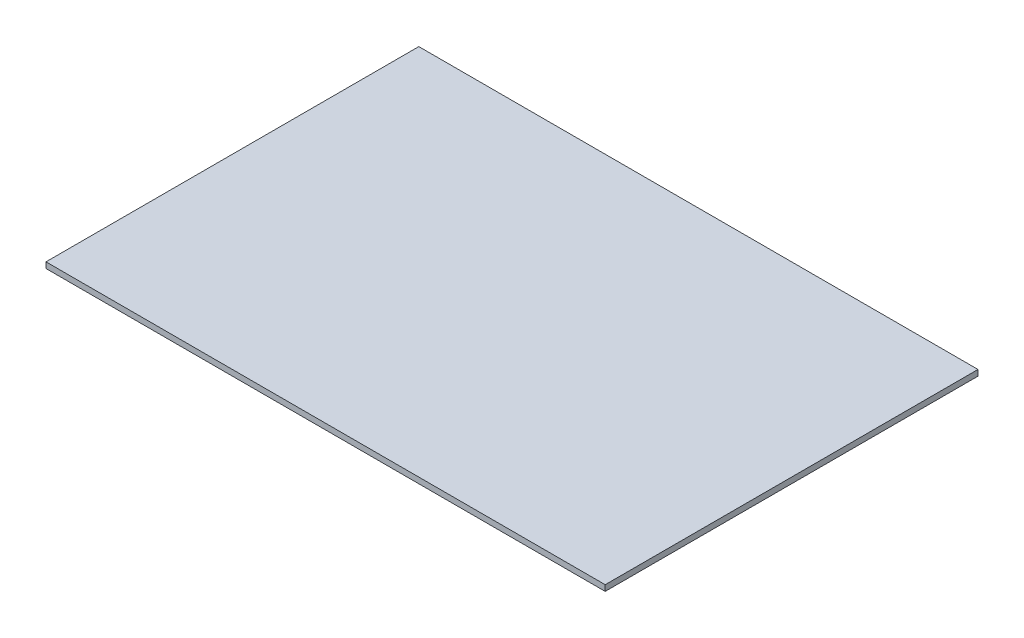
SolidWorks part; units mm, degrees
ref_plane "Front Plane" through (0, 0, 0) normal (0, 0, 1) x (1, 0, 0)
ref_plane "Top Plane" through (0, 0, 0) normal (0, 1, 0) x (1, 0, 0)
ref_plane "Right Plane" through (0, 0, 0) normal (1, 0, 0) x (0, 0, -1)
sketch "Sketch1" plane through (0, 0, 0) normal (0, 1, 0) x (1, 0, 0)
  line L1 (152.4, -101.6) -> (-152.4, -101.6)
  line L2 (152.4, -101.6) -> (152.4, 101.6)
  line L3 (152.4, 101.6) -> (-152.4, 101.6)
  line L4 (-152.4, -101.6) -> (-152.4, 101.6)
  line L5 (152.4, -101.6) -> (-152.4, 101.6) construction
  line L6 (152.4, 101.6) -> (-152.4, -101.6) construction
  point P0 (0, 0)
  dimension "D1" = 203.2
  dimension "D2" = 304.8
extrude "Boss-Extrude1" add sketch "Sketch1" along normal blind 3.175
